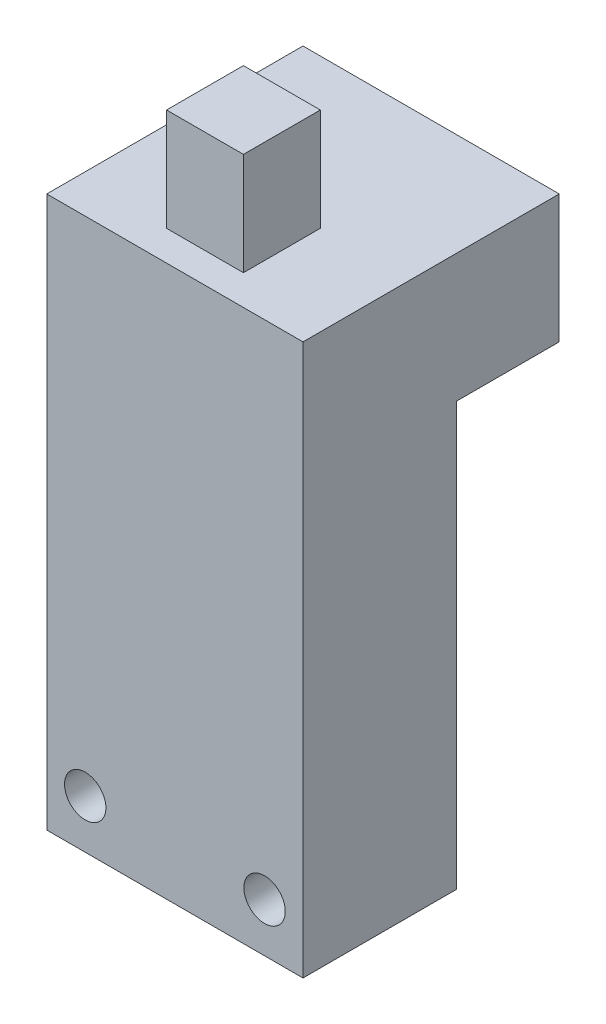
SolidWorks part; units mm, degrees
ref_plane "Front Plane" through (0, 0, 0) normal (0, 0, 1) x (1, 0, 0)
ref_plane "Top Plane" through (0, 0, 0) normal (0, 1, 0) x (1, 0, 0)
ref_plane "Right Plane" through (0, 0, 0) normal (1, 0, 0) x (0, 0, -1)
sketch "Sketch1" plane through (0, 0, 0) normal (0, 1, 0) x (1, 0, 0)
  line L1 (0, 0) -> (20, 0)
  line L2 (0, 0) -> (0, 20)
  line L3 (0, 20) -> (20, 20)
  line L4 (20, 0) -> (20, 20)
  dimension "D1" = 20
extrude "Boss-Extrude1" add sketch "Sketch1" along normal blind 10
sketch "Sketch2" plane through (0, 10, 0) normal (0, 1, 0) x (1, 0, 0)
  line L0 (10, 0) -> (10, 20) construction
  line L1 (0, 0) -> (20, 0) construction
  line L2 (20, 20) -> (0, 20) construction
  line L4 (7, 8.35) -> (13, 8.35)
  line L5 (7, 8.35) -> (7, 2.35)
  line L6 (7, 2.35) -> (13, 2.35)
  line L7 (13, 8.35) -> (13, 2.35)
  point P10 (10, 2.35)
  point P11 (13, 2.995)
  point P12 (7, 5.35)
  dimension "D1" = 6
  dimension "D2" = 5.35
extrude "Boss-Extrude2" add sketch "Sketch2" along normal blind 8
sketch "Sketch3" plane through (0, 0, 0) normal (0, -1, 0) x (1, 0, 0)
  line L0 (20, 0) -> (20, -20) construction
  line L1 (0, 0) -> (20, 0)
  line L2 (0, 0) -> (0, -12)
  line L3 (0, -12) -> (20, -12)
  line L4 (20, 0) -> (20, -12)
  dimension "D1" = 12
extrude "Boss-Extrude3" add sketch "Sketch3" along normal blind 33
sketch "Sketch4" plane through (0, 0, 0) normal (0, 0, 1) x (1, 0, 0)
  line L0 (17, -29.2) -> (20, -29.2) construction
  line L1 (20, 10) -> (20, -33) construction
  line L2 (3, -29.2) -> (0, -29.2) construction
  line L3 (0, 10) -> (0, -33) construction
  line L4 (20, -33) -> (0, -33) construction
  circle A0 centre (17, -29.2) radius 1.615
  circle A1 centre (3, -29.2) radius 1.615
  dimension "D1" = 3.23
  dimension "D2" = 3
  dimension "D3" = 3.8
extrude "Cut-Extrude1" cut sketch "Sketch4" against normal through all
